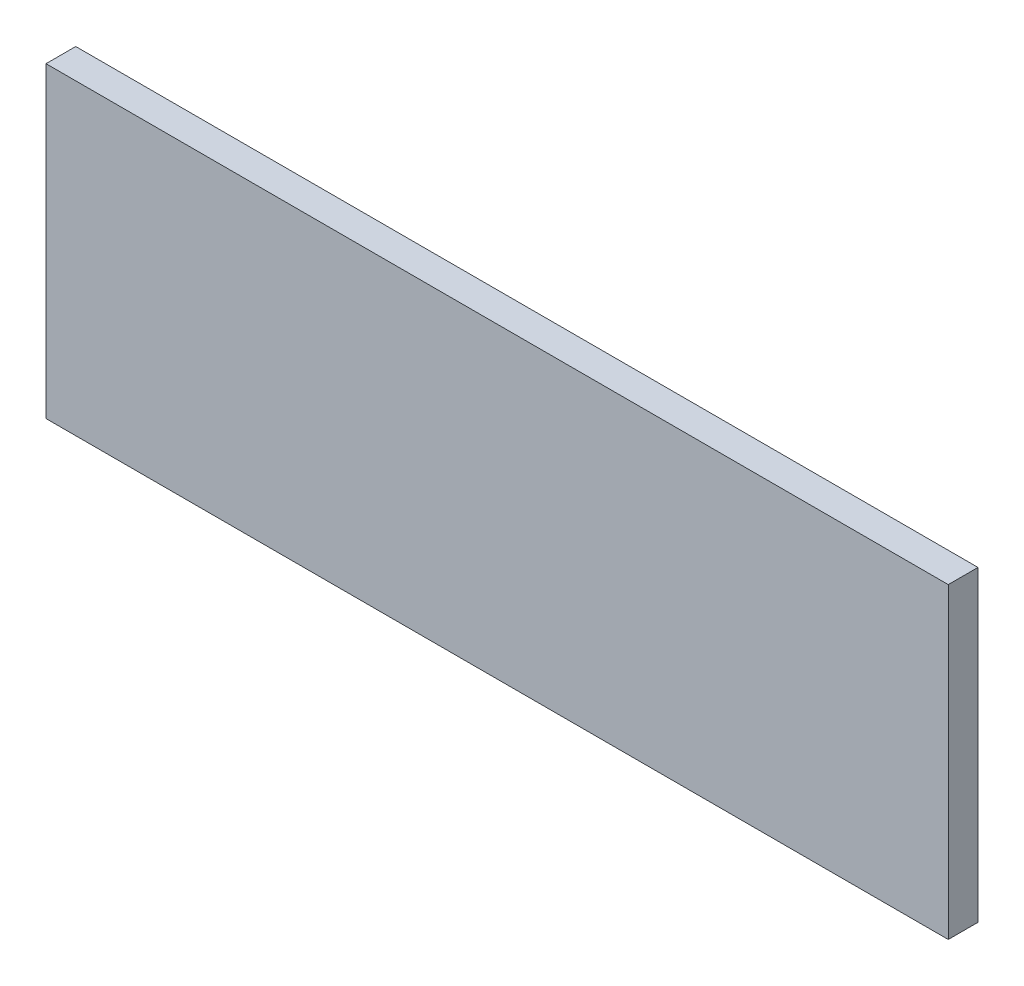
SolidWorks part; units mm, degrees
ref_plane "Plan de face" through (0, 0, 0) normal (0, 0, 1) x (1, 0, 0)
ref_plane "Plan de dessus" through (0, 0, 0) normal (0, 1, 0) x (1, 0, 0)
ref_plane "Plan de droite" through (0, 0, 0) normal (1, 0, 0) x (0, 0, -1)
sketch "Esquisse1" plane through (0, 0, 0) normal (0, 0, 1) x (1, 0, 0)
  line L1 (-45.5, 15.5) -> (45.5, 15.5)
  line L2 (-45.5, 15.5) -> (-45.5, -15.5)
  line L3 (-45.5, -15.5) -> (45.5, -15.5)
  line L4 (45.5, 15.5) -> (45.5, -15.5)
  line L5 (-45.5, 15.5) -> (45.5, -15.5) construction
  line L6 (-45.5, -15.5) -> (45.5, 15.5) construction
  point P0 (0, 0)
  dimension "D1" = 31
  dimension "D2" = 91
extrude "Boss.-Extru.1" add sketch "Esquisse1" along normal blind 3
